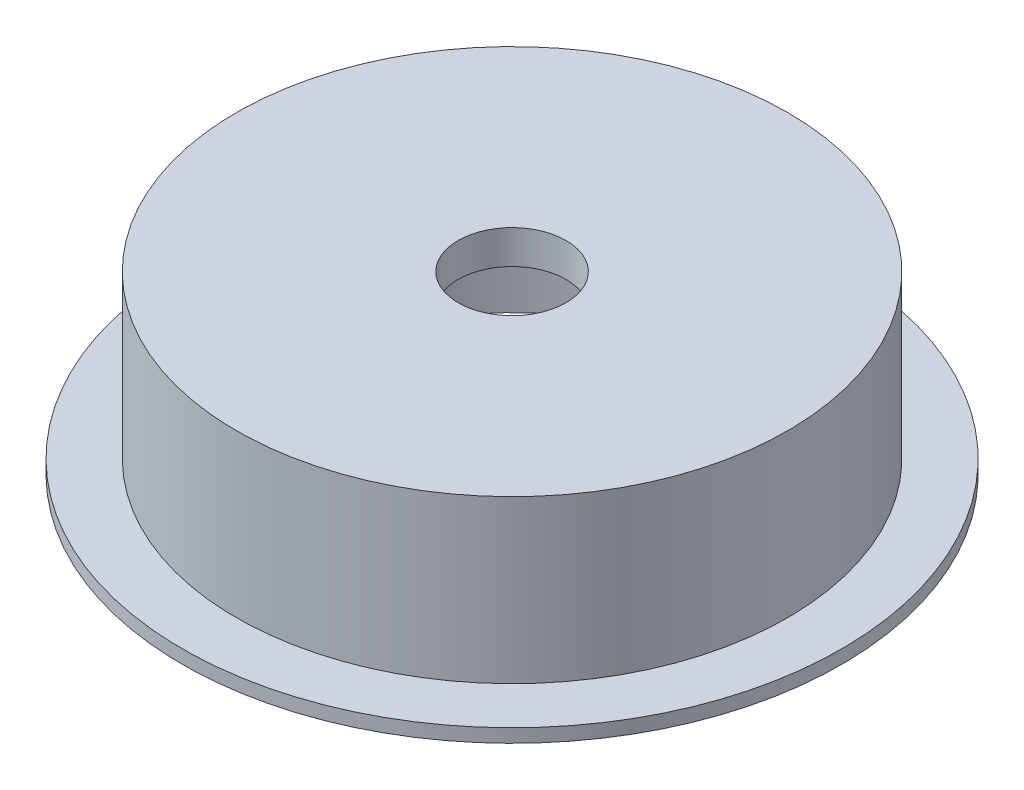
SolidWorks part; units mm, degrees
material "Сталь ШХ15 ГОСТ 801-78"
ref_plane "Plane1" through (0, 0, 0) normal (0, 0, 1) x (1, 0, 0)
ref_plane "Plane2" through (0, 0, 0) normal (0, 1, 0) x (1, 0, 0)
ref_plane "Plane3" through (0, 0, 0) normal (1, 0, 0) x (0, 0, -1)
sketch "Эскиз1" plane through (0, 0, 0) normal (0, 0, 1) x (1, 0, 0)
  line L0 (0, 0) -> (0, 42.3011) construction
  line L9 (17, 0) -> (18, 0)
  line L10 (18, 0) -> (18, 1.6476)
  line L11 (18, 1.6476) -> (24.4325, 1.6476)
  line L12 (24.4325, 1.6476) -> (24.4325, 2.6476)
  line L13 (24.4325, 2.6476) -> (20.4325, 2.6476)
  line L14 (20.4325, 2.6476) -> (20.4325, 14.6553)
  line L15 (20.4325, 14.6553) -> (4, 14.6553)
  line L16 (4, 14.6553) -> (4, 12.1553)
  line L17 (4, 12.1553) -> (17, 12.1553)
  line L18 (17, 12.1553) -> (17, 0)
  dimension "D1" = 1
  dimension "D2" = 1
  dimension "D3" = 4
  dimension "D4" = 18
  dimension "D5" = 4
  dimension "D6" = 2.5
revolve "Повернуть1" add sketch "Эскиз1" angle 360 about L0
